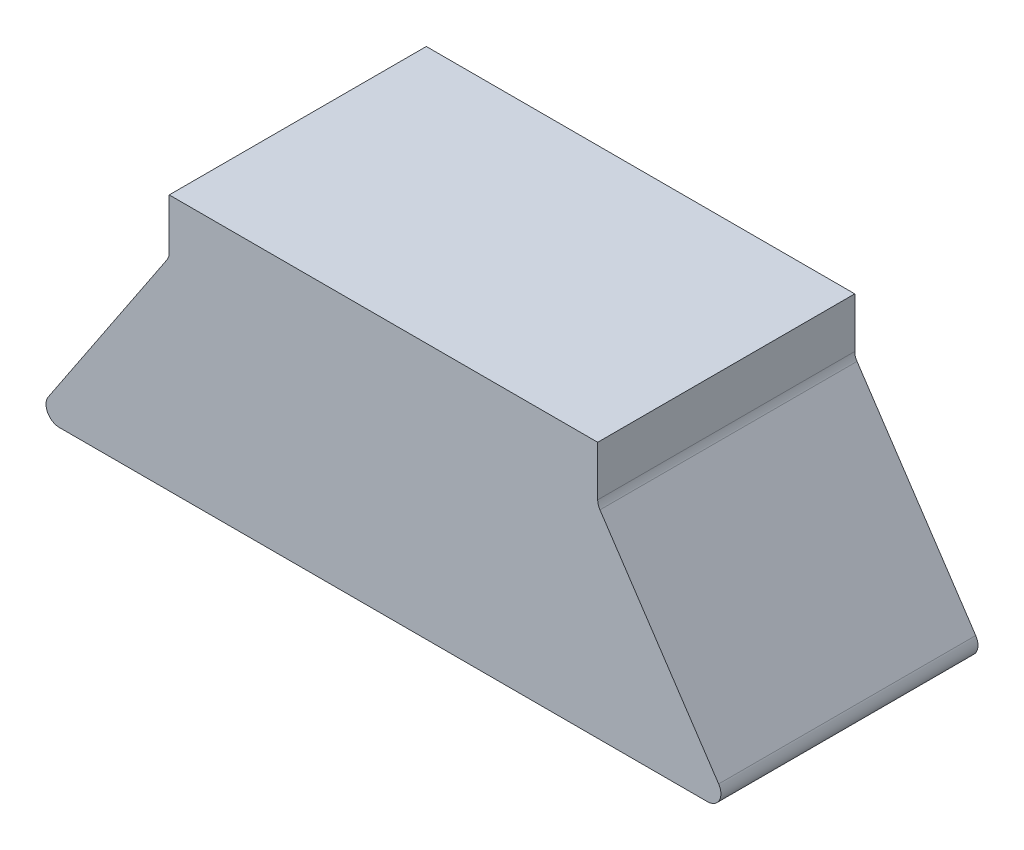
SolidWorks part; units mm, degrees
material "Copper"
ref_plane "Front Plane" through (0, 0, 0) normal (0, 0, 1) x (1, 0, 0)
ref_plane "Top Plane" through (0, 0, 0) normal (0, 1, 0) x (1, 0, 0)
ref_plane "Right Plane" through (0, 0, 0) normal (1, 0, 0) x (0, 0, -1)
sketch "Sketch1" plane through (0, 0, 0) normal (0, 0, 1) x (1, 0, 0)
  line L1 (-15.875, -9.5) -> (15.875, -9.5)
  line L2 (-15.875, -9.5) -> (-15.875, 9.5)
  line L3 (-15.875, 9.5) -> (15.875, 9.5)
  line L4 (15.875, -9.5) -> (15.875, 9.5)
  line L5 (-15.875, -9.5) -> (15.875, 9.5) construction
  line L6 (-15.875, 9.5) -> (15.875, -9.5) construction
  point P0 (0, 0)
  dimension "D1" = 31.75
  dimension "D2" = 19
extrude "Boss-Extrude1" add sketch "Sketch1" along normal mid plane 19.05
sketch "Sketch3" plane through (0, 0, 9.525) normal (0, 0, 1) x (1, 0, 0)
  line L0 (-15.875, -9.5) -> (-25.875, -9.5)
  line L1 (-25.875, -9.5) -> (-15.875, 5.5)
  line L2 (-15.875, 9.5) -> (-15.875, -9.5) construction
  line L3 (-15.875, 5.5) -> (-15.875, -9.5)
  line L4 (15.875, -9.5) -> (15.875, 5.5)
  line L5 (15.875, -9.5) -> (15.875, 9.5) construction
  line L6 (15.875, 5.5) -> (25.875, -9.5)
  line L7 (25.875, -9.5) -> (15.875, -9.5)
  line L8 (-15.875, 5.5) -> (15.875, 5.5) construction
  line L9 (15.875, 9.5) -> (-15.875, 9.5) construction
  dimension "D1" = 4
  dimension "D2" = 10
extrude "Boss-Extrude2" add sketch "Sketch3" against normal up to surface (19.05 mm away) up to face at (0, 0, -9.525)
fillet "Fillet5" radius 1 4 edges at (25.875, -9.5, 0) (-25.875, -9.5, 0) (-15.875, 5.5, 0) (15.875, 5.5, 0)
